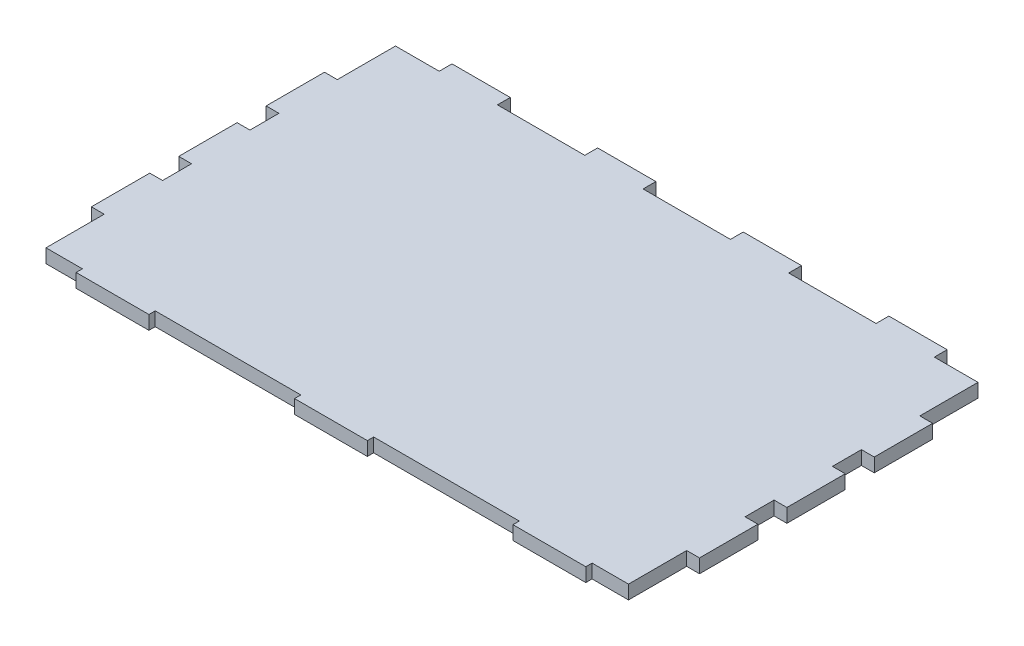
SolidWorks part; units mm, degrees
material "Balsa"
ref_plane "Front Plane" through (0, 0, 0) normal (0, 0, 1) x (1, 0, 0)
ref_plane "Top Plane" through (0, 0, 0) normal (0, 1, 0) x (1, 0, 0)
ref_plane "Right Plane" through (0, 0, 0) normal (1, 0, 0) x (0, 0, -1)
sketch "Sketch1" plane through (0, 0, 0) normal (0, 1, 0) x (1, 0, 0)
  line L1 (-127, -76.2) -> (127, -76.2)
  line L2 (-127, -76.2) -> (-127, 76.2)
  line L3 (-127, 76.2) -> (127, 76.2)
  line L4 (127, -76.2) -> (127, 76.2)
  point P4 (0, 76.2)
  point P6 (127, 0)
  dimension "D1" = 254
  dimension "D2" = 152.4
extrude "Boss-Extrude1" add sketch "Sketch1" along normal blind 6
sketch "Sketch2" plane through (0, 6, 0) normal (0, 1, 0) x (1, 0, 0)
  line L0 (0, 76.2) -> (0, -76.2) construction
  line L1 (127, 76.2) -> (-127, 76.2) construction
  line L2 (-127, 0) -> (127, 0) construction
  line L3 (-127, 76.2) -> (-127, -76.2) construction
  line L4 (127, -76.2) -> (127, 76.2) construction
  line L5 (-127, -76.2) -> (127, -76.2) construction
  line L6 (107.95, 76.2) -> (107.95, 81.788)
  line L7 (-19.05, 76.2) -> (-44.45, 76.2)
  line L8 (-19.05, 76.2) -> (-19.05, 81.788)
  line L9 (-19.05, 81.788) -> (-44.45, 81.788)
  line L10 (-44.45, 76.2) -> (-44.45, 81.788)
  line L11 (-82.55, 76.2) -> (-107.95, 76.2)
  line L12 (-82.55, 76.2) -> (-82.55, 81.788)
  line L13 (-82.55, 81.788) -> (-107.95, 81.788)
  line L14 (-107.95, 76.2) -> (-107.95, 81.788)
  line L15 (82.55, 81.788) -> (107.95, 81.788)
  line L16 (82.55, 76.2) -> (82.55, 81.788)
  line L17 (82.55, 76.2) -> (107.95, 76.2)
  line L18 (44.45, 76.2) -> (44.45, 81.788)
  line L19 (19.05, 81.788) -> (44.45, 81.788)
  line L20 (19.05, 76.2) -> (19.05, 81.788)
  line L21 (19.05, 76.2) -> (44.45, 76.2)
  line L38 (79.375, -78.9432) -> (111.125, -78.9432)
  line L39 (-15.875, -76.2) -> (15.875, -76.2)
  line L40 (-15.875, -76.2) -> (-15.875, -78.9432)
  line L41 (-15.875, -78.9432) -> (15.875, -78.9432)
  line L42 (15.875, -76.2) -> (15.875, -78.9432)
  line L43 (111.125, -76.2) -> (111.125, -78.9432)
  line L44 (79.375, -76.2) -> (111.125, -76.2)
  line L45 (79.375, -76.2) -> (79.375, -78.9432)
  line L46 (-15.875, -78.9432) -> (15.875, -78.9432)
  line L47 (15.875, -76.2) -> (15.875, -78.9432)
  line L48 (-15.875, -76.2) -> (15.875, -76.2)
  line L49 (-15.875, -76.2) -> (-15.875, -78.9432)
  line L50 (-111.125, -78.9432) -> (-79.375, -78.9432)
  line L51 (-79.375, -76.2) -> (-79.375, -78.9432)
  line L52 (-111.125, -76.2) -> (-79.375, -76.2)
  line L53 (-111.125, -76.2) -> (-111.125, -78.9432)
  point P21 (-95.25, 81.788)
  point P22 (-31.75, 81.788)
  point P35 (0, -78.9432)
  point P36 (-95.25, -78.9432)
  point P37 (95.25, -78.9432)
  line M12 (127, 76.2) -> (-127, 76.2)
  dimension "D1" = 25.4
  dimension "D2" = 63.5
  dimension "D3" = 63.5
  dimension "D4" = 5.588
  dimension "D5" = 31.75
  dimension "D6" = 2.7432
  dimension "D9" = 95.25
  dimension "D10" = 95.25
  dimension "D7" = 2
  dimension "D8" = 2
extrude "Tabs - Top/Bottom" add sketch "Sketch2" against normal up to surface (6 mm away) contours L16 L6 L15 M12 | L11 L14 L13 L12 | L7 L10 L9 L8 | L21 L18 L19 L20 | L50 L51 L52 L53 | L41 L42 L39 L40 | L38 L43 L44 L45 up to face at (0, 0, 0)
sketch "Sketch3" plane through (0, 6, 0) normal (0, 1, 0) x (1, 0, 0)
  line L0 (-127, 0) -> (127, 0) construction
  line L1 (-127, 76.2) -> (-127, -76.2) construction
  line L2 (127, -76.2) -> (127, 76.2) construction
  line L3 (-132.588, -25.3746) -> (-132.588, -50.8254)
  line L4 (-127, -12.7254) -> (-132.588, -12.7254)
  line L5 (-127, -12.7254) -> (-127, 12.7254)
  line L6 (-127, 12.7254) -> (-132.588, 12.7254)
  line L7 (-132.588, -12.7254) -> (-132.588, 12.7254)
  line L8 (-127, 25.3746) -> (-132.588, 25.3746)
  line L9 (-127, 25.3746) -> (-127, 50.8254)
  line L10 (-127, 50.8254) -> (-132.588, 50.8254)
  line L11 (-132.588, 25.3746) -> (-132.588, 50.8254)
  line L12 (-127, -50.8254) -> (-132.588, -50.8254)
  line L13 (-127, -25.3746) -> (-127, -50.8254)
  line L14 (-127, -25.3746) -> (-132.588, -25.3746)
  line L15 (0, 76.2) -> (0, -76.2) construction
  line L16 (19.05, 76.2) -> (-19.05, 76.2) construction
  line L18 (127, -25.3746) -> (132.588, -25.3746)
  line L19 (127, -25.3746) -> (127, -50.8254)
  line L20 (127, -50.8254) -> (132.588, -50.8254)
  line L21 (132.588, 25.3746) -> (132.588, 50.8254)
  line L22 (127, 50.8254) -> (132.588, 50.8254)
  line L23 (127, 25.3746) -> (127, 50.8254)
  line L24 (127, 25.3746) -> (132.588, 25.3746)
  line L25 (132.588, -12.7254) -> (132.588, 12.7254)
  line L26 (127, 12.7254) -> (132.588, 12.7254)
  line L27 (127, -12.7254) -> (127, 12.7254)
  line L28 (127, -12.7254) -> (132.588, -12.7254)
  line L29 (132.588, -25.3746) -> (132.588, -50.8254)
  point P14 (-132.588, 0)
  point P15 (-132.588, 38.1)
  dimension "D1" = 25.4508
  dimension "D2" = 38.1
  dimension "D3" = 5.588
extrude "Tabs - Side" add sketch "Sketch3" against normal up to surface (6 mm away) up to face at (0, 0, -10.4077)
sketch "Sketch4" plane through (0, 6, 0) normal (0, 1, 0) x (1, 0, 0)
  line L56 (79.2734, -79.0448) -> (111.2266, -79.0448)
  line L57 (79.2734, -79.0448) -> (111.2266, -79.0448)
  line L58 (-79.2734, -76.3016) -> (-15.9766, -76.3016)
  line L59 (-79.2734, -76.3016) -> (-15.9766, -76.3016)
  line L60 (-15.9766, -76.3016) -> (-15.9766, -79.0448)
  line L61 (-15.9766, -76.3016) -> (-15.9766, -79.0448)
  line L62 (15.9766, -79.0448) -> (15.9766, -76.3016)
  line L63 (15.9766, -79.0448) -> (15.9766, -76.3016)
  line L64 (15.9766, -76.3016) -> (79.2734, -76.3016)
  line L65 (15.9766, -76.3016) -> (79.2734, -76.3016)
  line L66 (111.2266, -76.3016) -> (127.1016, -76.3016)
  line L67 (111.2266, -76.3016) -> (127.1016, -76.3016)
  line L68 (108.0516, 76.3016) -> (108.0516, 81.8896)
  line L69 (108.0516, 76.3016) -> (108.0516, 81.8896)
  line L70 (108.0516, 81.8896) -> (82.4484, 81.8896)
  line L71 (108.0516, 81.8896) -> (82.4484, 81.8896)
  line L72 (82.4484, 81.8896) -> (82.4484, 76.3016)
  line L73 (82.4484, 81.8896) -> (82.4484, 76.3016)
  line L74 (82.4484, 76.3016) -> (44.5516, 76.3016)
  line L75 (82.4484, 76.3016) -> (44.5516, 76.3016)
  line L76 (44.5516, 76.3016) -> (44.5516, 81.8896)
  line L77 (44.5516, 76.3016) -> (44.5516, 81.8896)
  line L78 (44.5516, 81.8896) -> (18.9484, 81.8896)
  line L79 (44.5516, 81.8896) -> (18.9484, 81.8896)
  line L80 (18.9484, 81.8896) -> (18.9484, 76.3016)
  line L81 (18.9484, 81.8896) -> (18.9484, 76.3016)
  line L82 (18.9484, 76.3016) -> (-18.9484, 76.3016)
  line L83 (18.9484, 76.3016) -> (-18.9484, 76.3016)
  line L84 (-18.9484, 76.3016) -> (-18.9484, 81.8896)
  line L85 (-18.9484, 76.3016) -> (-18.9484, 81.8896)
  line L86 (-18.9484, 81.8896) -> (-44.5516, 81.8896)
  line L87 (-18.9484, 81.8896) -> (-44.5516, 81.8896)
  line L88 (-44.5516, 81.8896) -> (-44.5516, 76.3016)
  line L89 (-44.5516, 81.8896) -> (-44.5516, 76.3016)
  line L90 (-44.5516, 76.3016) -> (-82.4484, 76.3016)
  line L91 (-44.5516, 76.3016) -> (-82.4484, 76.3016)
  line L92 (-82.4484, 76.3016) -> (-82.4484, 81.8896)
  line L93 (-82.4484, 76.3016) -> (-82.4484, 81.8896)
  line L94 (-82.4484, 81.8896) -> (-108.0516, 81.8896)
  line L95 (-82.4484, 81.8896) -> (-108.0516, 81.8896)
  line L96 (-108.0516, 81.8896) -> (-108.0516, 76.3016)
  line L97 (-108.0516, 81.8896) -> (-108.0516, 76.3016)
  line L98 (-108.0516, 76.3016) -> (-127.1016, 76.3016)
  line L99 (-108.0516, 76.3016) -> (-127.1016, 76.3016)
  line L100 (-111.2266, -76.3016) -> (-111.2266, -79.0448)
  line L101 (-111.2266, -76.3016) -> (-111.2266, -79.0448)
  line L102 (-111.2266, -79.0448) -> (-79.2734, -79.0448)
  line L103 (-111.2266, -79.0448) -> (-79.2734, -79.0448)
  line L104 (-79.2734, -79.0448) -> (-79.2734, -76.3016)
  line L105 (-79.2734, -79.0448) -> (-79.2734, -76.3016)
  line L106 (-15.9766, -79.0448) -> (15.9766, -79.0448)
  line L107 (-15.9766, -79.0448) -> (15.9766, -79.0448)
  line L108 (79.2734, -76.3016) -> (79.2734, -79.0448)
  line L109 (79.2734, -76.3016) -> (79.2734, -79.0448)
  line L110 (111.2266, -79.0448) -> (111.2266, -76.3016)
  line L111 (111.2266, -79.0448) -> (111.2266, -76.3016)
  line L120 (-127.1016, 76.3016) -> (-127.1016, 50.927)
  line L121 (-127.1016, 50.927) -> (-132.6896, 50.927)
  line L122 (-132.6896, 50.927) -> (-132.6896, 25.273)
  line L123 (-132.6896, 25.273) -> (-127.1016, 25.273)
  line L124 (-127.1016, 25.273) -> (-127.1016, 12.827)
  line L125 (-127.1016, 12.827) -> (-132.6896, 12.827)
  line L126 (-132.6896, 12.827) -> (-132.6896, -12.827)
  line L127 (-132.6896, -12.827) -> (-127.1016, -12.827)
  line L128 (-127.1016, -12.827) -> (-127.1016, -25.273)
  line L129 (-127.1016, -25.273) -> (-132.6896, -25.273)
  line L130 (-132.6896, -25.273) -> (-132.6896, -50.927)
  line L131 (-132.6896, -50.927) -> (-127.1016, -50.927)
  line L132 (-127.1016, -50.927) -> (-127.1016, -76.3016)
  line L133 (-127.1016, -76.3016) -> (-111.2266, -76.3016)
  line L150 (127.1016, -76.3016) -> (127.1016, -50.927)
  line L151 (127.1016, -50.927) -> (132.6896, -50.927)
  line L152 (132.6896, -50.927) -> (132.6896, -25.273)
  line L153 (132.6896, -25.273) -> (127.1016, -25.273)
  line L154 (127.1016, -25.273) -> (127.1016, -12.827)
  line L155 (127.1016, -12.827) -> (132.6896, -12.827)
  line L156 (132.6896, -12.827) -> (132.6896, 12.827)
  line L157 (132.6896, 12.827) -> (127.1016, 12.827)
  line L158 (127.1016, 12.827) -> (127.1016, 25.273)
  line L159 (127.1016, 25.273) -> (132.6896, 25.273)
  line L160 (132.6896, 25.273) -> (132.6896, 50.927)
  line L161 (132.6896, 50.927) -> (127.1016, 50.927)
  line L162 (127.1016, 50.927) -> (127.1016, 76.3016)
  line L163 (127.1016, 76.3016) -> (108.0516, 76.3016)
  line L180 (-127.1016, 76.3016) -> (-127.1016, 50.927)
  line L181 (-127.1016, 50.927) -> (-132.6896, 50.927)
  line L182 (-132.6896, 50.927) -> (-132.6896, 25.273)
  line L183 (-132.6896, 25.273) -> (-127.1016, 25.273)
  line L184 (-127.1016, 25.273) -> (-127.1016, 12.827)
  line L185 (-127.1016, 12.827) -> (-132.6896, 12.827)
  line L186 (-132.6896, 12.827) -> (-132.6896, -12.827)
  line L187 (-132.6896, -12.827) -> (-127.1016, -12.827)
  line L188 (-127.1016, -12.827) -> (-127.1016, -25.273)
  line L189 (-127.1016, -25.273) -> (-132.6896, -25.273)
  line L190 (-132.6896, -25.273) -> (-132.6896, -50.927)
  line L191 (-132.6896, -50.927) -> (-127.1016, -50.927)
  line L192 (-127.1016, -50.927) -> (-127.1016, -76.3016)
  line L193 (-127.1016, -76.3016) -> (-111.2266, -76.3016)
  line L210 (127.1016, -76.3016) -> (127.1016, -50.927)
  line L211 (127.1016, -50.927) -> (132.6896, -50.927)
  line L212 (132.6896, -50.927) -> (132.6896, -25.273)
  line L213 (132.6896, -25.273) -> (127.1016, -25.273)
  line L214 (127.1016, -25.273) -> (127.1016, -12.827)
  line L215 (127.1016, -12.827) -> (132.6896, -12.827)
  line L216 (132.6896, -12.827) -> (132.6896, 12.827)
  line L217 (132.6896, 12.827) -> (127.1016, 12.827)
  line L218 (127.1016, 12.827) -> (127.1016, 25.273)
  line L219 (127.1016, 25.273) -> (132.6896, 25.273)
  line L220 (132.6896, 25.273) -> (132.6896, 50.927)
  line L221 (132.6896, 50.927) -> (127.1016, 50.927)
  line L222 (127.1016, 50.927) -> (127.1016, 76.3016)
  line L223 (127.1016, 76.3016) -> (108.0516, 76.3016)
  dimension "D1" = 0.1016
extrude "KERF" [suppressed] add sketch "Sketch4" against normal up to surface (6 mm away)
